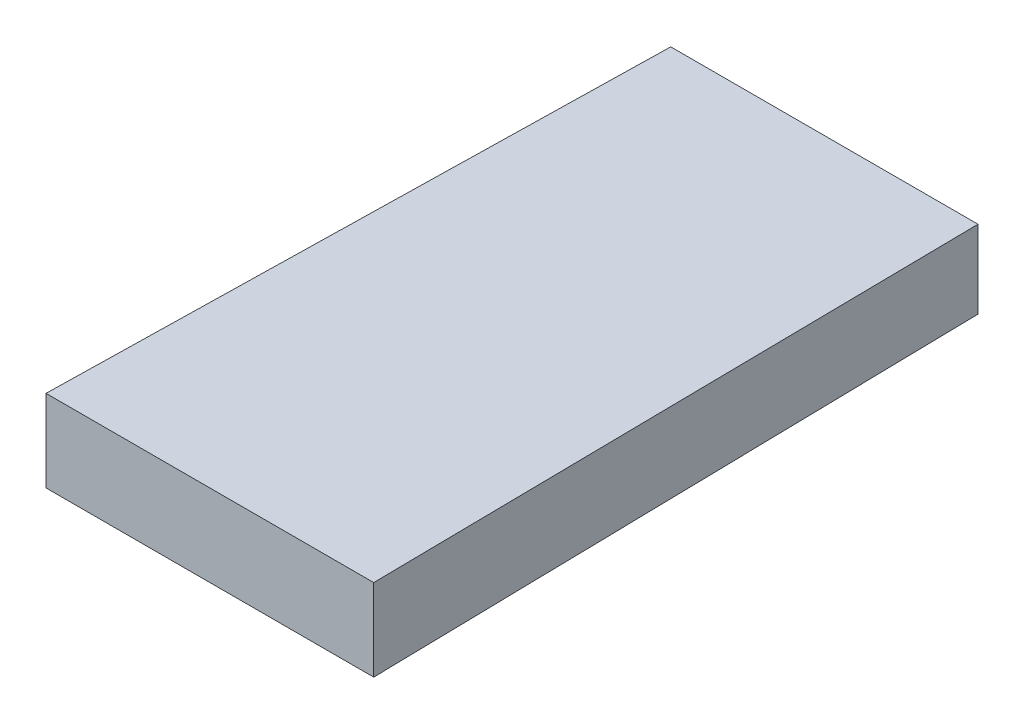
SolidWorks part; units mm, degrees
ref_plane "Front Plane" through (0, 0, 0) normal (0, 0, 1) x (1, 0, 0)
ref_plane "Top Plane" through (0, 0, 0) normal (0, 1, 0) x (1, 0, 0)
ref_plane "Right Plane" through (0, 0, 0) normal (1, 0, 0) x (0, 0, -1)
sketch "Sketch3" plane through (0, 0, 0) normal (0, 0, 1) x (1, 0, 0)
  line L1 (-75, 19) -> (75, 19)
  line L2 (-75, 19) -> (-75, -19)
  line L3 (-75, -19) -> (75, -19)
  line L4 (75, 19) -> (75, -19)
  line L5 (-75, 19) -> (75, -19) construction
  line L6 (-75, -19) -> (75, 19) construction
  point P0 (0, 0)
  dimension "D1" = 150
  dimension "D2" = 38
ref_plane "Plane1" through (0, 0, 300) normal (0, 0, 1) x (1, 0, 0)
sketch "Sketch4" plane through (0, 0, 300) normal (0, 0, 1) x (1, 0, 0)
  line L1 (-80, 20) -> (80, 20)
  line L2 (-80, 20) -> (-80, -20)
  line L3 (-80, -20) -> (80, -20)
  line L4 (80, 20) -> (80, -20)
  line L5 (-80, 20) -> (80, -20) construction
  line L6 (-80, -20) -> (80, 20) construction
  point P0 (0, 0)
  dimension "D1" = 160
  dimension "D2" = 40
loft "Loft1" add profiles "Sketch3", "Sketch4"
sketch "Sketch5" plane through (0, 0, 300) normal (0, 0, 1) x (1, 0, 0)
  line L0 (0, 20) -> (0, -20)
  line L1 (80, 20) -> (-80, 20) construction
  line L2 (-80, -20) -> (80, -20) construction
  line L3 (80, 20) -> (-80, 20)
  line L4 (80, 0) -> (-80, 0)
  line L5 (-80, 20) -> (-80, -20) construction
  circle A1 centre (-60, 0) radius 20
  circle A3 centre (-20, 0) radius 20
  circle A5 centre (20, 0) radius 20
  circle A7 centre (60, 0) radius 20
  point P10 (0, 20)
  point P16 (0, 0)
ref_plane "Plane2" through (75, 0, 0) normal (1, 0, 0) x (0, 0, -1)
sketch "Sketch6" plane through (75, 0, 0) normal (1, 0, 0) x (0, 0, -1)
  circle A0 centre (-211.0591, 0) radius 18.5
